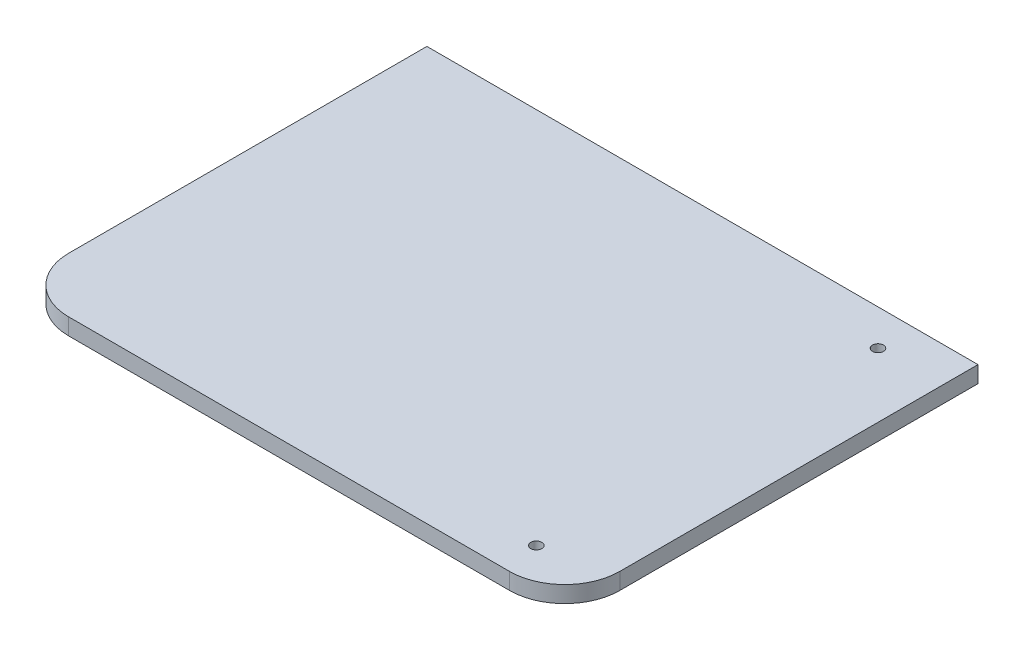
SolidWorks part; units mm, degrees
ref_plane "Front Plane" through (0, 0, 0) normal (0, 0, 1) x (1, 0, 0)
ref_plane "Top Plane" through (0, 0, 0) normal (0, 1, 0) x (1, 0, 0)
ref_plane "Right Plane" through (0, 0, 0) normal (1, 0, 0) x (0, 0, -1)
sketch "Sketch1" plane through (0, 0, 0) normal (0, 1, 0) x (1, 0, 0)
  line L1 (-50, 37.5) -> (50, 37.5)
  line L2 (-50, 37.5) -> (-50, -37.5)
  line L3 (-50, -37.5) -> (50, -37.5)
  line L4 (50, 37.5) -> (50, -37.5)
  line L5 (-50, 37.5) -> (50, -37.5) construction
  line L6 (-50, -37.5) -> (50, 37.5) construction
  point P0 (0, 0)
extrude "Boss-Extrude1" add sketch "Sketch1" along normal blind 3
fillet "Fillet1" radius 10 2 edges at (50, 1.5, 37.5) (-50, 1.5, 37.5)
sketch "Sketch2" plane through (0, 3, 0) normal (0, 1, 0) x (1, 0, 0)
  circle A0 centre (38.3512, -31) radius 1
  dimension "D1" = 31
extrude "Cut-Extrude1" cut sketch "Sketch2" against normal through all
mirror "Mirror1" about plane through (0, 0, 0) normal (0, 0, 1) of "Cut-Extrude1"
